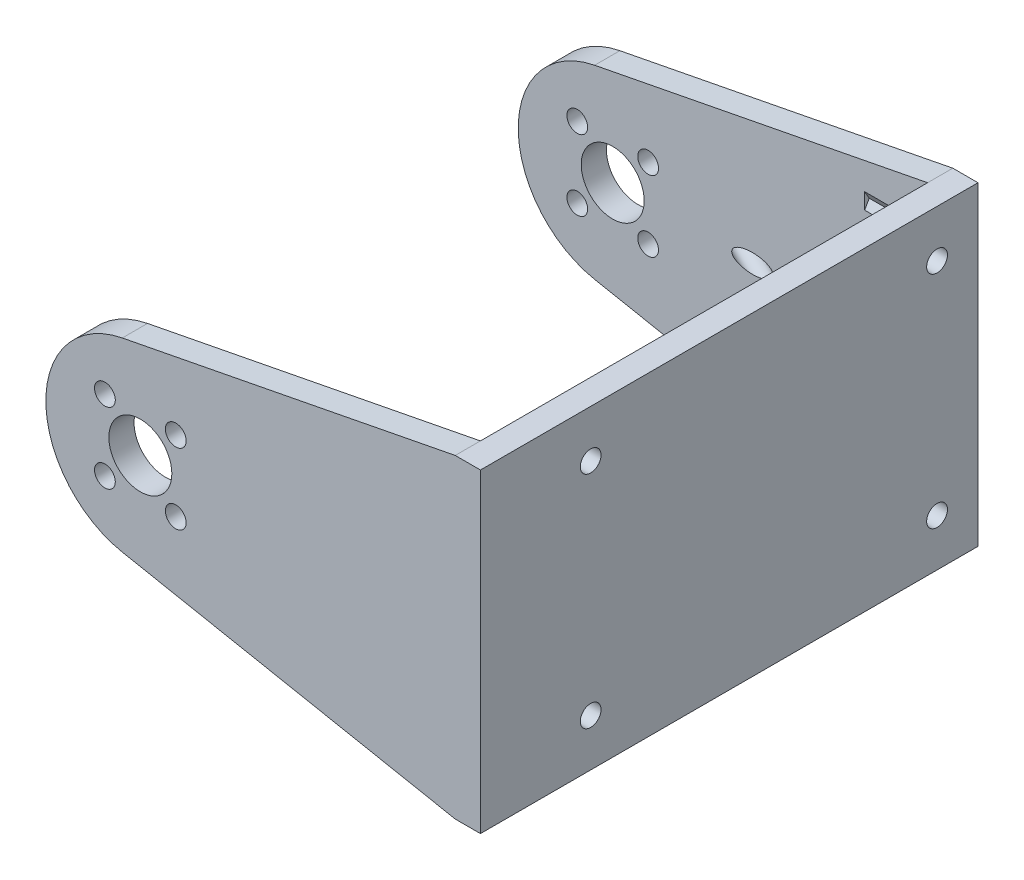
SolidWorks part; units mm, degrees
ref_plane "前视基准面" through (0, 0, 0) normal (0, 0, 1) x (1, 0, 0)
ref_plane "上视基准面" through (0, 0, 0) normal (0, 1, 0) x (1, 0, 0)
ref_plane "右视基准面" through (0, 0, 0) normal (1, 0, 0) x (0, 0, -1)
sketch "草图2" plane through (0, 0, 0) normal (1, 0, 0) x (0, 0, -1)
  line L1 (-39.5, -25) -> (39.5, -25)
  line L2 (-39.5, -25) -> (-39.5, 25)
  line L3 (-39.5, 25) -> (39.5, 25)
  line L4 (39.5, -25) -> (39.5, 25)
  line L5 (-39.5, -25) -> (39.5, 25) construction
  line L6 (-39.5, 25) -> (39.5, -25) construction
  point P0 (0, 0)
  dimension "D1" = 79
  dimension "D2" = 50
extrude "凸台-拉伸1" add sketch "草图2" along normal blind 4
sketch "草图3" plane through (0, 0, 39.5) normal (0, 0, 1) x (1, 0, 0)
  line L0 (-52.8622, 14.7244) -> (0, 25)
  line L1 (0, 25) -> (0, -25)
  line L2 (0, -25) -> (-52.8622, -14.7244)
  line L4 (-55.625, -5.625) -> (-44.375, -5.625) construction
  line L5 (-55.625, -5.625) -> (-55.625, 5.625) construction
  line L6 (-55.625, 5.625) -> (-44.375, 5.625) construction
  line L7 (-44.375, -5.625) -> (-44.375, 5.625) construction
  line L8 (-55.625, -5.625) -> (-44.375, 5.625) construction
  line L9 (-55.625, 5.625) -> (-44.375, -5.625) construction
  arc A0 (-52.8622, 14.7244) -> (-52.8622, -14.7244) centre (-50, 0) ccw
  circle A1 centre (-50, 0) radius 5
  circle A2 centre (-55.625, 5.625) radius 1.65
  circle A3 centre (-44.375, 5.625) radius 1.65
  circle A4 centre (-44.375, -5.625) radius 1.65
  circle A5 centre (-55.625, -5.625) radius 1.65
  dimension "D2" = 15
  dimension "D3" = 3.3
  dimension "D4" = 10
  dimension "D1" = 50
  dimension "D5" = 11.25
extrude "凸台-拉伸2" add sketch "草图3" against normal blind 4
mirror "镜向1" about plane through (0, 0, 0) normal (0, 0, 1) of "凸台-拉伸2"
sketch "草图4" plane through (0, 0, 0) normal (-1, 0, 0) x (0, 0, 1)
  line L0 (-9.6, -12.6) -> (-9.6, 12.6)
  line L1 (-8, -11) -> (8, -11)
  line L2 (-8, -11) -> (-8, 11)
  line L3 (-8, 11) -> (8, 11)
  line L4 (8, -11) -> (8, 11)
  line L5 (-8, -11) -> (8, 11) construction
  line L6 (-8, 11) -> (8, -11) construction
  line L7 (-9.6, 12.6) -> (9.6, 12.6)
  line L8 (9.6, -12.6) -> (9.6, 12.6)
  line L9 (-9.6, -12.6) -> (9.6, -12.6)
  point P0 (0, 0)
  dimension "D2" = 22
  dimension "D3" = 16
  dimension "D1" = 1.6
extrude "凸台-拉伸3" add sketch "草图4" along normal blind 6
sketch "草图5" plane through (-6, 0, 0) normal (-1, 0, 0) x (0, 0, 1)
  line L9 (0, 0) -> (0, 15.7892) construction
  line L22 (0, 0) -> (15.1194, 0) construction
  line L37 (8, -11) -> (8, 11) construction
  line L38 (12, 9.25) -> (9.6, 9.25)
  line L39 (9.6, -12.6) -> (9.6, 12.6) construction
  line L40 (9.6, 9.25) -> (9.6, 4.75)
  line L41 (9.6, 4.75) -> (12, 4.75)
  line L42 (9.6, -9.25) -> (9.6, -4.75)
  line L43 (12, -9.25) -> (9.6, -9.25)
  line L44 (9.6, -4.75) -> (12, -4.75)
  line L45 (-12, -9.25) -> (-9.6, -9.25)
  line L46 (-9.6, -4.75) -> (-12, -4.75)
  line L47 (-9.6, -9.25) -> (-9.6, -4.75)
  line L48 (-9.6, 9.25) -> (-9.6, 4.75)
  line L49 (-12, 9.25) -> (-9.6, 9.25)
  line L50 (-9.6, 4.75) -> (-12, 4.75)
  arc A10 (12, 4.75) -> (12, 9.25) centre (12, 7) ccw
  circle A11 centre (12, 7) radius 1.1
  circle A18 centre (12, -7) radius 1.1
  arc A19 (12, -4.75) -> (12, -9.25) centre (12, -7) cw
  circle A20 centre (-12, 7) radius 1.1
  circle A21 centre (-12, -7) radius 1.1
  arc A22 (-12, -4.75) -> (-12, -9.25) centre (-12, -7) ccw
  arc A23 (-12, 4.75) -> (-12, 9.25) centre (-12, 7) cw
  point P0 (12, 6)
  dimension "D1" = 7
  dimension "D5" = 4.5
  dimension "D6" = 2.2
  dimension "D2" = 4
extrude "凸台-拉伸4" add sketch "草图5" against normal blind 2
sketch "草图6" plane through (0, 0, -8) normal (0, 0, 1) x (1, 0, 0)
  line L1 (-6, -4.75) -> (-6, 4.75) construction
  circle A0 centre (-6, 0) radius 1.15
  point P2 (-6, 0)
  dimension "D1" = 2.3
extrude "切除-拉伸1" cut sketch "草图6" against normal blind 2
ref_plane "基准面1" through (-12.8025, 0, -6.5232) normal (0.891, 0, 0.454) x (0, 1, 0)
sketch "草图7" plane through (-12.8025, 0, -6.5232) normal (0.891, 0, 0.454) x (0, 1, 0)
  line L0 (-25, -37.0107) -> (25, -37.0107) construction
  circle A0 centre (0, -19.0107) radius 1.5
  dimension "D2" = 3
  dimension "D1" = 18
extrude "切除-拉伸2" cut sketch "草图7" against normal blind 69
sketch "草图8" plane through (0, 0, 0) normal (-1, 0, 0) x (0, 0, 1)
  line L1 (-33, -17.5) -> (22, -17.5) construction
  line L2 (-33, -17.5) -> (-33, 17.5) construction
  line L3 (-33, 17.5) -> (22, 17.5) construction
  line L4 (22, -17.5) -> (22, 17.5) construction
  line L5 (-33, -17.5) -> (22, 17.5) construction
  line L6 (-33, 17.5) -> (22, -17.5) construction
  circle A0 centre (-33, 17.5) radius 1.65
  circle A1 centre (22, 17.5) radius 1.65
  circle A2 centre (22, -17.5) radius 1.65
  circle A3 centre (-33, -17.5) radius 1.65
  point P0 (-5.5, 0)
  dimension "D1" = 3.3
  dimension "D2" = 55
  dimension "D3" = 35
  dimension "D4" = 5.5
extrude "切除-拉伸3" cut sketch "草图8" against normal through all
sketch "草图9" plane through (0, 0, 0) normal (-1, 0, 0) x (0, 0, 1)
  line L1 (-31.3834, 14.7) -> (-29.7668, 17.5)
  line L2 (-29.7668, 17.5) -> (-31.3834, 20.3)
  line L3 (-31.3834, 20.3) -> (-34.6166, 20.3)
  line L4 (-34.6166, 20.3) -> (-36.2332, 17.5)
  line L5 (-36.2332, 17.5) -> (-34.6166, 14.7)
  line L6 (-34.6166, 14.7) -> (-31.3834, 14.7)
  line L7 (-29.7668, -17.5) -> (-31.3834, -14.7)
  line L8 (-31.3834, -14.7) -> (-34.6166, -14.7)
  line L9 (-34.6166, -14.7) -> (-36.2332, -17.5)
  line L10 (-36.2332, -17.5) -> (-34.6166, -20.3)
  line L11 (-34.6166, -20.3) -> (-31.3834, -20.3)
  line L12 (-31.3834, -20.3) -> (-29.7668, -17.5)
  line L13 (23.6166, -14.7) -> (20.3834, -14.7)
  line L14 (20.3834, -14.7) -> (18.7668, -17.5)
  line L15 (18.7668, -17.5) -> (20.3834, -20.3)
  line L16 (20.3834, -20.3) -> (23.6166, -20.3)
  line L17 (23.6166, -20.3) -> (25.2332, -17.5)
  line L18 (25.2332, -17.5) -> (23.6166, -14.7)
  line L19 (25.2332, 17.5) -> (23.6166, 20.3)
  line L20 (23.6166, 20.3) -> (20.3834, 20.3)
  line L21 (20.3834, 20.3) -> (18.7668, 17.5)
  line L22 (18.7668, 17.5) -> (20.3834, 14.7)
  line L23 (20.3834, 14.7) -> (23.6166, 14.7)
  line L24 (23.6166, 14.7) -> (25.2332, 17.5)
  circle A0 centre (-33, 17.5) radius 2.8 construction
  circle A1 centre (-33, -17.5) radius 2.8 construction
  circle A2 centre (22, -17.5) radius 2.8 construction
  circle A3 centre (22, 17.5) radius 2.8 construction
  dimension "D1" = 5.6
extrude "切除-拉伸4" cut sketch "草图9" along normal blind 10 and the other way blind 0.7
